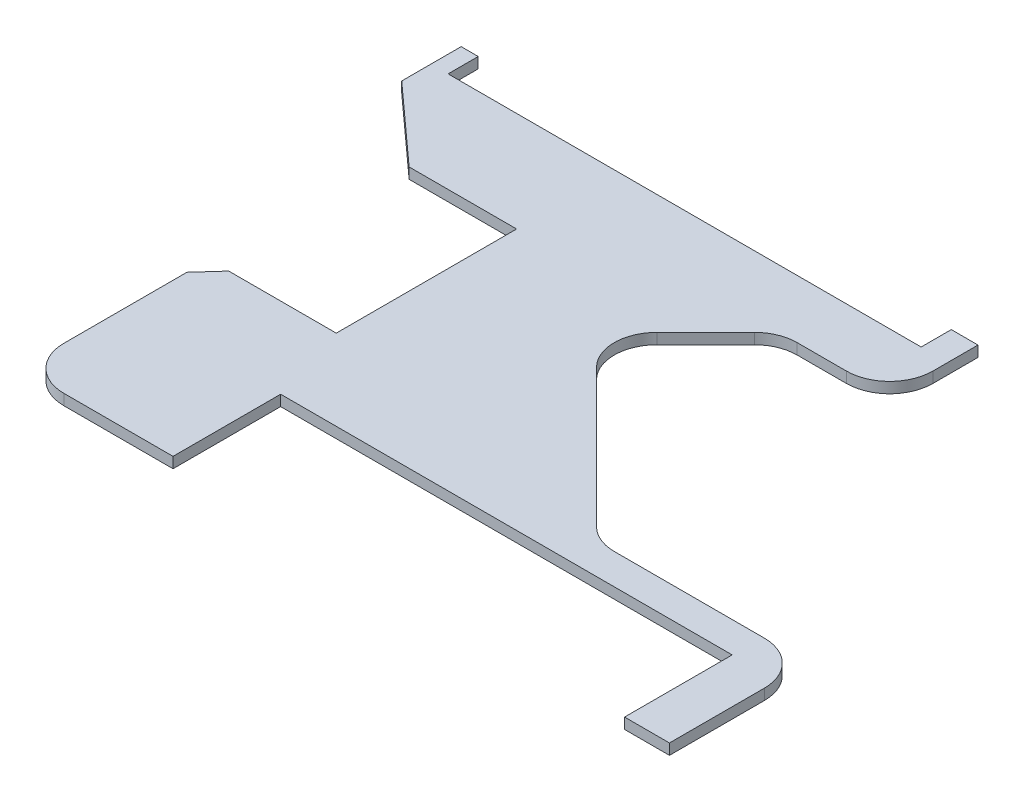
SolidWorks part; units mm, degrees
ref_plane "Front Plane" through (0, 0, 0) normal (0, 0, 1) x (1, 0, 0)
ref_plane "Top Plane" through (0, 0, 0) normal (0, 1, 0) x (1, 0, 0)
ref_plane "Right Plane" through (0, 0, 0) normal (1, 0, 0) x (0, 0, -1)
sketch "Sketch2" plane through (0, 0, 0) normal (0, 1, 0) x (1, 0, 0)
  line L0 (0, 0) -> (0, 133.731) construction
  line L1 (0, 133.731) -> (139.7, 133.731)
  line L2 (0, 133.731) -> (-139.7, 133.731)
  line L3 (-139.7, 133.731) -> (-139.7, 151.511)
  line L4 (139.7, 133.731) -> (139.7, 151.511)
  line L5 (-139.7, 151.511) -> (139.7, 151.511) construction
  line L6 (0, 0) -> (0, -79.121) construction
  line L7 (0, -79.121) -> (241.3, -79.121)
  line L8 (0, -79.121) -> (-25.4, -79.121)
  line L9 (241.3, -79.121) -> (241.3, -142.621)
  line L10 (-25.4, -79.121) -> (-25.4, -142.621)
  line L11 (241.3, -142.621) -> (-25.4, -142.621) construction
  line L12 (0, 0) -> (-39.9542, 0) construction
  line L13 (-39.9542, 0) -> (-39.9542, -31.75)
  line L14 (-39.9542, 0) -> (-39.9542, 74.93)
  line L15 (-39.9542, 74.93) -> (-103.4542, 74.93)
  line L16 (-39.9542, -31.75) -> (-103.4542, -31.75)
  line L17 (-103.4542, 74.93) -> (-103.4542, -31.75) construction
  line L18 (-153.6667, 155.0775) -> (210.7402, 155.0775)
  line L19 (146.7958, 79.9366) -> (210.7402, 79.9366)
  line L20 (146.7958, 79.9366) -> (100.3333, 12.8375)
  line L21 (100.3333, 12.8375) -> (158.0989, -27.162)
  line L22 (158.0989, -27.162) -> (273.8693, -27.162)
  line L23 (273.8693, -149.7225) -> (-153.6667, -149.7225)
  line L24 (-153.6667, -149.7225) -> (-153.6667, 155.0775)
  line L25 (-139.7, 151.511) -> (-149.5068, 151.511)
  line L26 (-149.5068, 116.6173) -> (-103.4542, 74.93)
  line L27 (-149.5068, 116.6173) -> (-149.5068, 151.511)
  line L28 (-115.1217, -44.6393) -> (-103.4542, -31.75)
  line L29 (-115.1217, -44.6393) -> (-115.1217, -117.221)
  line L30 (-89.7217, -142.621) -> (-25.4, -142.621)
  line L31 (-25.4, -142.621) -> (-25.7489, -142.6783)
  line L32 (139.7, 151.511) -> (155.2079, 151.511)
  line L33 (155.2079, 151.511) -> (155.2079, 125.0375)
  line L34 (82.7696, 92.198) -> (54.0905, 63.519)
  line L35 (54.0905, 27.5979) -> (135.5486, -53.8602)
  line L36 (153.5091, -61.2997) -> (242.1259, -61.2997)
  line L37 (267.5259, -86.6997) -> (267.5259, -142.621)
  line L38 (267.5259, -142.621) -> (241.3, -142.621)
  line L39 (100.7301, 99.6375) -> (129.8079, 99.6375)
  line L40 (273.8693, -27.162) -> (273.8693, -149.7225)
  line L41 (210.7402, 155.0775) -> (210.7402, 79.9366)
  line L42 (-25.273, -79.248) -> (-25.273, -142.748)
  line L43 (0, -79.248) -> (-25.273, -79.248)
  line L44 (0, -79.248) -> (241.173, -79.248)
  line L45 (241.173, -79.248) -> (241.173, -142.748)
  line L46 (267.6529, -142.748) -> (241.173, -142.748)
  line L47 (267.6529, -86.6997) -> (267.6529, -142.748)
  line L48 (153.5091, -61.1727) -> (242.1259, -61.1727)
  line L49 (54.1803, 27.6877) -> (135.6384, -53.7704)
  line L50 (82.8594, 92.1082) -> (54.1803, 63.4292)
  line L51 (100.7301, 99.5105) -> (129.8079, 99.5105)
  line L52 (155.3349, 151.638) -> (155.3349, 125.0375)
  line L53 (139.573, 151.638) -> (155.3349, 151.638)
  line L54 (139.573, 133.858) -> (139.573, 151.638)
  line L55 (0, 133.858) -> (139.573, 133.858)
  line L56 (0, 133.858) -> (-139.573, 133.858)
  line L57 (-139.573, 133.858) -> (-139.573, 151.638)
  line L58 (-139.573, 151.638) -> (-149.6338, 151.638)
  line L59 (-149.6338, 116.561) -> (-149.6338, 151.638)
  line L60 (-149.6338, 116.561) -> (-103.5031, 74.803)
  line L61 (-40.0812, 74.803) -> (-103.5031, 74.803)
  line L62 (-40.0812, 0) -> (-40.0812, 74.803)
  line L63 (-40.0812, 0) -> (-40.0812, -31.623)
  line L64 (-40.0812, -31.623) -> (-103.5105, -31.623)
  line L65 (-115.2487, -44.5903) -> (-103.5105, -31.623)
  line L66 (-115.2487, -44.5903) -> (-115.2487, -117.221)
  line L67 (-89.7217, -142.748) -> (-25.273, -142.748)
  circle A0 centre (0, 0) radius 4.7625
  arc A1 (-89.7217, -142.621) -> (-115.1217, -117.221) centre (-89.7217, -117.221) cw
  arc A2 (242.1259, -61.2997) -> (267.5259, -86.6997) centre (242.1259, -86.6997) cw
  arc A3 (135.5486, -53.8602) -> (153.5091, -61.2997) centre (153.5091, -35.8997) ccw
  arc A4 (54.0905, 27.5979) -> (54.0905, 63.519) centre (72.051, 45.5584) cw
  arc A5 (129.8079, 99.6375) -> (155.2079, 125.0375) centre (129.8079, 125.0375) ccw
  arc A6 (100.7301, 99.6375) -> (82.7696, 92.198) centre (100.7301, 74.2375) ccw
  arc A7 (242.1259, -61.1727) -> (267.6529, -86.6997) centre (242.1259, -86.6997) cw
  arc A8 (135.6384, -53.7704) -> (153.5091, -61.1727) centre (153.5091, -35.8997) ccw
  arc A9 (54.1803, 27.6877) -> (54.1803, 63.4292) centre (72.051, 45.5584) cw
  arc A10 (100.7301, 99.5105) -> (82.8594, 92.1082) centre (100.7301, 74.2375) ccw
  arc A11 (129.8079, 99.5105) -> (155.3349, 125.0375) centre (129.8079, 125.0375) ccw
  arc A12 (-89.7217, -142.748) -> (-115.2487, -117.221) centre (-89.7217, -117.221) cw
  dimension "D4" = 9.525
  dimension "D17" = 25.4
  dimension "D18" = 25.4
  dimension "D1" = 279.4
  dimension "D2" = 133.731
  dimension "D3" = 17.78
  dimension "D5" = 25.4
  dimension "D6" = 266.7
  dimension "D7" = 79.121
  dimension "D8" = 63.5
  dimension "D9" = 31.75
  dimension "D10" = 106.68
  dimension "D11" = 63.5
  dimension "D12" = 39.9542
  dimension "D13" = 0.127
  dimension "D15" = 304.8
  dimension "D19" = 254
  dimension "D20" = 142.24
extrude "Boss-Extrude1" add sketch "Sketch2" along normal blind 6.35 contours L59 L58 L57 L56 L55 L54 L53 L52 A11 L51 A10 L50 A9 L49 A8 L48 A7 L47 L46 L45 L44 L43 L42 L67 A12 L66 L65 L64 L63 L62 L61 L60
